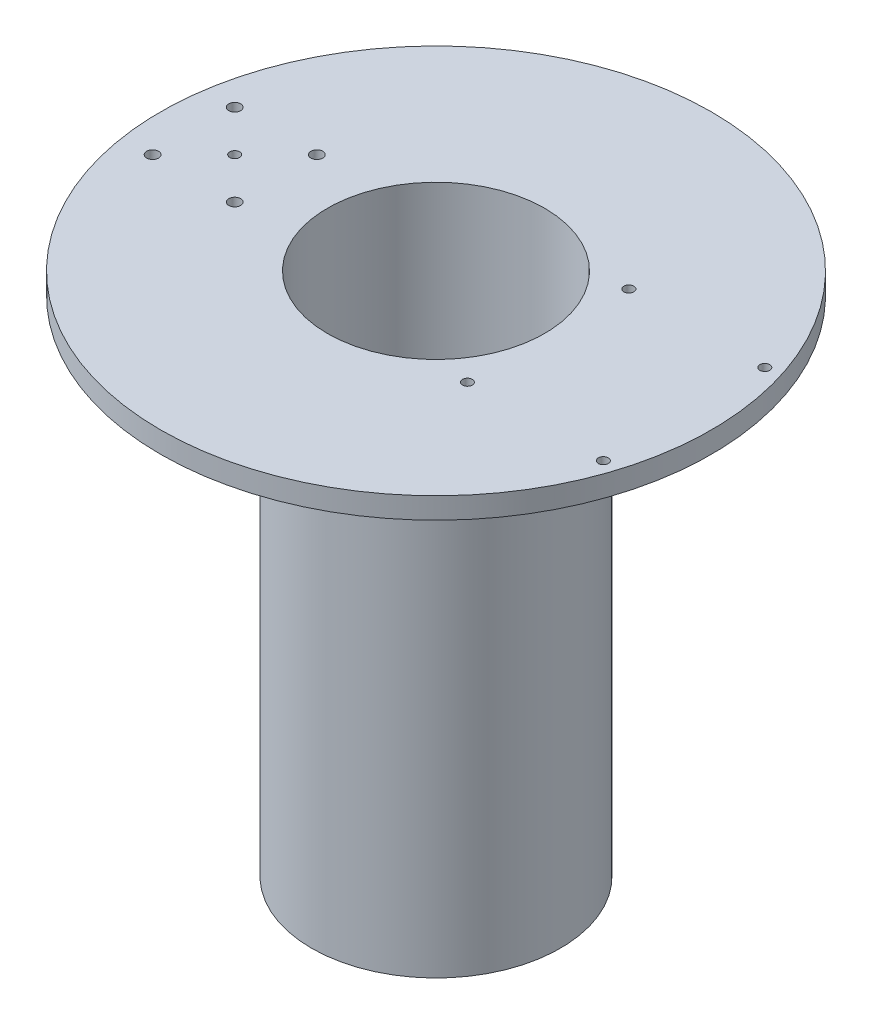
SolidWorks part; units mm, degrees
ref_plane "Front Plane" through (0, 0, 0) normal (0, 0, 1) x (1, 0, 0)
ref_plane "Top Plane" through (0, 0, 0) normal (0, 1, 0) x (1, 0, 0)
ref_plane "Right Plane" through (0, 0, 0) normal (1, 0, 0) x (0, 0, -1)
sketch "Sketch1" plane through (0, 0, 0) normal (0, 0, 1) x (1, 0, 0)
  line L0 (0, 0) -> (57, 0)
  line L1 (57, 0) -> (57, -190)
  line L2 (57, -190) -> (104, -190)
  line L3 (104, -190) -> (104, -185)
  line L4 (104, -185) -> (63, -185)
  line L5 (63, -185) -> (63, 8)
  line L6 (63, 8) -> (0, 8)
  line L7 (0, 8) -> (0, 0)
  point P3 (31.5, 8)
  dimension "D1" = 190
  dimension "D2" = 8
  dimension "D3" = 5
  dimension "D4" = 6
  dimension "D5" = 57
  dimension "D6" = 41
revolve "Revolve1" add sketch "Sketch1" angle 360 about L3
ref_plane "Plane1" through (0, 0, 0) normal (0, 0, 1) x (1, 0, 0)
ref_plane "Plane2" through (102, 0, 0) normal (1, 0, 0) x (0, 0, -1)
sketch "Sketch3" plane through (0, 8, 0) normal (0, 1, 0) x (1, 0, 0)
  line L1 (146.346, 30.48) -> (197.654, 30.48)
  line L2 (146.346, 30.48) -> (146.346, -30.48)
  line L3 (146.346, -30.48) -> (197.654, -30.48)
  line L4 (197.654, 30.48) -> (197.654, -30.48)
  line L5 (146.346, 30.48) -> (197.654, -30.48) construction
  line L6 (146.346, -30.48) -> (197.654, 30.48) construction
  circle A0 centre (104, 0) radius 104 construction
  point P0 (172, 0)
  point P5 (197.654, 0)
  dimension "D1" = 60.96
  dimension "D2" = 51.308
  dimension "D3" = 68
hole_wizard "#10-24 Tapped Hole3" positions "Sketch8" profile "Sketch9" tap size "#10-24" standard "ANSI Inch" end condition through all
sketch "Sketch8" plane through (0, 8, 0) normal (0, 1, 0) x (1, 0, 0)
  point P0 (146.346, 30.48)
  point P3 (197.654, 30.48)
  point P6 (197.654, -30.48)
  point P9 (146.346, -30.48)
sketch "Sketch9" plane through (146.346, 8, -30.48) normal (1, 0, 0) x (0, 0, 1)
  line L0 (0, 0) -> (0, 198)
  line L1 (0, 198) -> (1.875, 198)
  line L2 (1.875, 198) -> (1.875, 0)
  line L5 (1.875, 0) -> (0, 0)
  line L11 (0, -6.35) -> (0, 107.95) construction
  dimension "Thru Tap Drill Dia." = 3.75
  dimension "Thru Tap Drill Depth" = 198
cosmetic thread "Hole Thread6"
cosmetic thread "Hole Thread7"
cosmetic thread "Hole Thread8"
cosmetic thread "Hole Thread9"
hole_wizard "#10-24 Tapped Hole4" positions "Sketch10" profile "Sketch11" tap size "#10-24" standard "ANSI Inch" end condition through all
sketch "Sketch10" plane through (0, 8, 0) normal (0, 1, 0) x (1, 0, 0)
  point P0 (28, 0)
  dimension "D1" = 28
sketch "Sketch11" plane through (28, 8, 0) normal (1, 0, 0) x (0, 0, 1)
  line L0 (0, 0) -> (0, 198)
  line L1 (0, 198) -> (1.875, 198)
  line L2 (1.875, 198) -> (1.875, 0)
  line L5 (1.875, 0) -> (0, 0)
  line L11 (0, -6.35) -> (0, 107.95) construction
  dimension "Thru Tap Drill Dia." = 3.75
  dimension "Thru Tap Drill Depth" = 198
cosmetic thread "Hole Thread10"
sketch "Sketch12" plane through (0, 8, 0) normal (0, 1, 0) x (1, 0, 0)
  line L1 (12.5, 15.5) -> (43.5, 15.5)
  line L2 (12.5, 15.5) -> (12.5, -15.5)
  line L3 (12.5, -15.5) -> (43.5, -15.5)
  line L4 (43.5, 15.5) -> (43.5, -15.5)
  line L5 (12.5, 15.5) -> (43.5, -15.5) construction
  line L6 (12.5, -15.5) -> (43.5, 15.5) construction
  point P0 (28, 0)
  dimension "D1" = 31
  dimension "D2" = 31
hole_wizard "#10-24 Tapped Hole5" positions "Sketch15" profile "Sketch14" tap size "#10-24" standard "ANSI Inch" end condition through all
sketch "Sketch15" plane through (0, 8, 0) normal (0, 1, 0) x (1, 0, 0)
  point P0 (12.5, 15.5)
  point P3 (43.5, 15.5)
  point P6 (43.5, -15.5)
  point P9 (12.5, -15.5)
sketch "Sketch14" plane through (12.5, 8, -15.5) normal (1, 0, 0) x (0, 0, 1)
  line L0 (0, 0) -> (0, 198)
  line L1 (0, 198) -> (2.25, 198)
  line L2 (2.25, 198) -> (2.25, 0)
  line L5 (2.25, 0) -> (0, 0)
  line L11 (0, -6.35) -> (0, 107.95) construction
  dimension "Thru Tap Drill Dia." = 4.5
  dimension "Thru Tap Drill Depth" = 198
cosmetic thread "Hole Thread11"
cosmetic thread "Hole Thread12"
cosmetic thread "Hole Thread13"
cosmetic thread "Hole Thread14"
sketch "Sketch20" plane through (0, -190, 0) normal (0, -1, 0) x (1, 0, 0)
  line L1 (79, 25) -> (129, 25)
  line L2 (79, 25) -> (79, -25)
  line L3 (79, -25) -> (129, -25)
  line L4 (129, 25) -> (129, -25)
  line L5 (79, 25) -> (129, -25) construction
  line L6 (79, -25) -> (129, 25) construction
  point P0 (104, 0)
  dimension "D1" = 50
  dimension "D2" = 50
hole_wizard "CBORE for M5 Cheese Head Screw1" positions "Sketch25" profile "Sketch26" counterbore size "M5" standard "AS" end condition through all
sketch "Sketch25" plane through (0, -190, 0) normal (0, -1, 0) x (-1, 0, 0)
  point P0 (-79, -25)
  point P3 (-79, 25)
  point P6 (-129, 25)
  point P9 (-129, -25)
sketch "Sketch26" plane through (79, -190, 25) normal (1, 0, 0) x (0, 0, -1)
  line L0 (0, 0) -> (0, 198)
  line L1 (0, 198) -> (2.75, 198)
  line L3 (2.75, 198) -> (2.75, 3.3)
  line L4 (2.75, 3.3) -> (4.75, 3.3)
  line L5 (4.75, 3.3) -> (4.75, 0)
  line L7 (4.75, 0) -> (0, 0)
  line L11 (0, -6.35) -> (0, 107.95) construction
  dimension "Thru Hole Dia." = 5.5
  dimension "Thru Hole Depth" = 198
  dimension "C'Bore Dia." = 9.5
  dimension "C'Bore Depth" = 3.3
